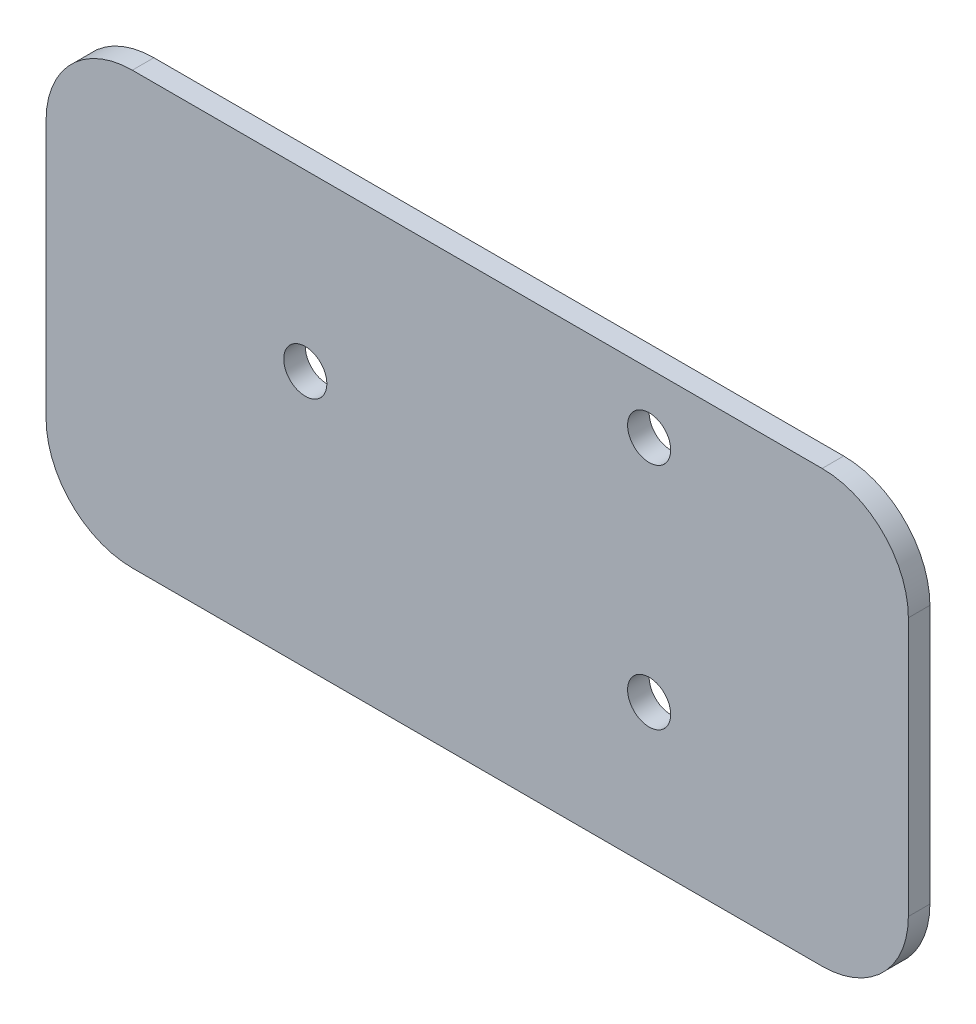
SolidWorks part; units mm, degrees
ref_plane "Front Plane" through (0, 0, 0) normal (0, 0, 1) x (1, 0, 0)
ref_plane "Top Plane" through (0, 0, 0) normal (0, 1, 0) x (1, 0, 0)
ref_plane "Right Plane" through (0, 0, 0) normal (1, 0, 0) x (0, 0, -1)
sketch "Sketch1" plane through (0, 0, 0) normal (0, 0, 1) x (1, 0, 0)
  line L0 (175.3841, 140.3257) -> (588.1705, 140.3257) construction
  line L1 (175.3841, 140.3257) -> (588.1705, 140.3257) construction
  line L2 (607.2205, 150.4857) -> (752.5141, 150.4857) construction
  line L3 (607.2205, 150.4857) -> (752.5141, 150.4857)
  line L4 (409.7794, 139.0557) -> (511.3794, 139.0557)
  line L5 (400.9171, 140.3257) -> (527.9171, 140.3257) construction
  line L6 (397.0794, 126.3557) -> (397.0794, 88.2557)
  line L7 (409.7794, 75.5557) -> (511.3794, 75.5557)
  line L8 (524.0794, 126.3557) -> (524.0794, 88.2557)
  line L9 (460.5794, 139.0557) -> (460.5794, 75.5557) construction
  line L10 (435.2555, 113.3793) -> (435.2555, 130.248) construction
  line L11 (435.2555, 130.248) -> (485.9032, 130.248) construction
  circle A0 centre (485.9032, 130.248) radius 3.175 construction
  circle A1 centre (485.9032, 130.248) radius 3.175
  circle A2 centre (485.9032, 96.5107) radius 3.175 construction
  circle A3 centre (435.2555, 113.3793) radius 3.175 construction
  circle A4 centre (485.9032, 96.5107) radius 3.175
  circle A5 centre (435.2555, 113.3793) radius 3.175
  arc A6 (511.3794, 139.0557) -> (524.0794, 126.3557) centre (511.3794, 126.3557) cw
  arc A7 (511.3794, 75.5557) -> (524.0794, 88.2557) centre (511.3794, 88.2557) ccw
  arc A8 (397.0794, 88.2557) -> (409.7794, 75.5557) centre (409.7794, 88.2557) ccw
  arc A9 (409.7794, 139.0557) -> (397.0794, 126.3557) centre (409.7794, 126.3557) ccw
  point P29 (460.5794, 130.248)
  dimension "D1" = 12.7
  dimension "D2" = 127
  dimension "D3" = 1.27
  dimension "D4" = 63.5
extrude "Boss-Extrude1" add sketch "Sketch1" along normal blind 3.175 contours L4 A9 L6 A8 L7 A7 L8 A6 A1 A4 A5
